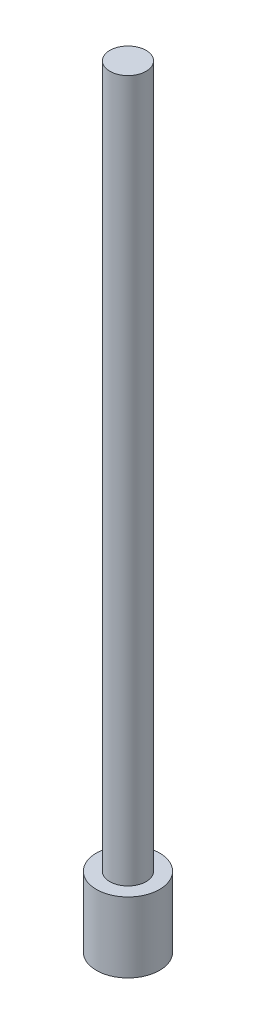
SolidWorks part; units mm, degrees
ref_plane "Front Plane" through (0, 0, 0) normal (0, 0, 1) x (1, 0, 0)
ref_plane "Top Plane" through (0, 0, 0) normal (0, 1, 0) x (1, 0, 0)
ref_plane "Right Plane" through (0, 0, 0) normal (1, 0, 0) x (0, 0, -1)
sketch "Sketch1" plane through (0, 0, 0) normal (0, 1, 0) x (1, 0, 0)
  circle A0 centre (0, 0) radius 7.75
  dimension "D1" = 15.5
extrude "Boss-Extrude1" add sketch "Sketch1" along normal blind 300 contours A0
sketch "Sketch2" plane through (0, 0, 0) normal (0, 1, 0) x (1, 0, 0)
  circle A0 centre (0, 0) radius 13.5
  dimension "D1" = 27
extrude "Boss-Extrude2" add sketch "Sketch2" against normal blind 30
